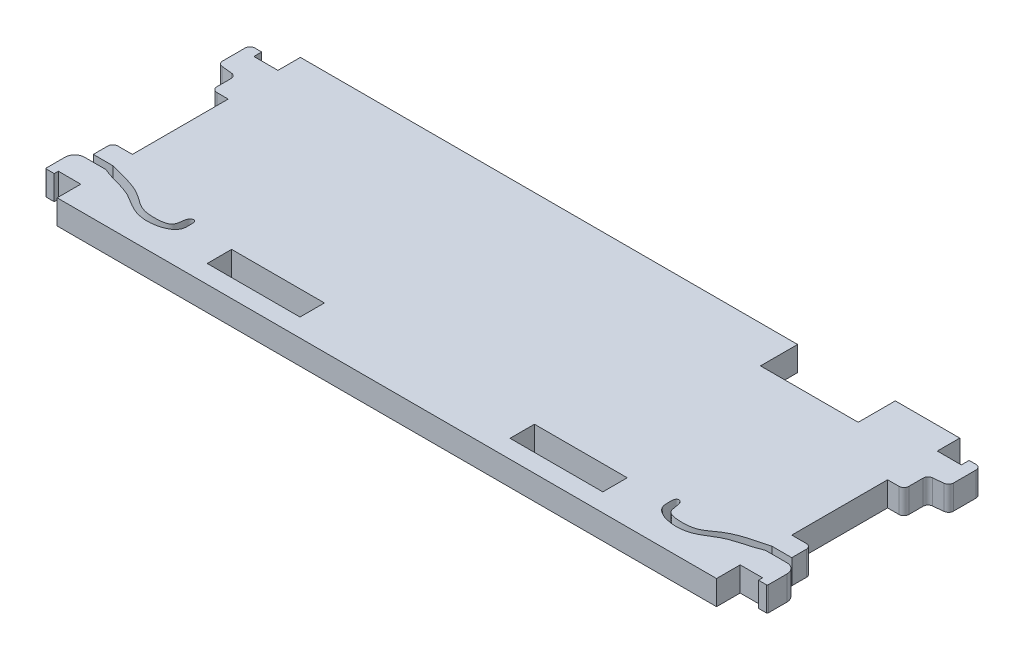
SolidWorks part; units mm, degrees
material "Custom Plastic"
ref_plane "Front Plane" through (0, 0, 0) normal (0, 0, 1) x (1, 0, 0)
ref_plane "Top Plane" through (0, 0, 0) normal (0, 1, 0) x (1, 0, 0)
ref_plane "Right Plane" through (0, 0, 0) normal (1, 0, 0) x (0, 0, -1)
sketch "Sketch1" plane through (0, 0, 0) normal (0, 1, 0) x (1, 0, 0)
  line L0 (34.4805, 15.8115) -> (34.4805, 10.9855)
  line L1 (-42.8625, -15.8115) -> (42.8625, -15.8115)
  line L2 (-42.8625, -15.8115) -> (-42.8625, -12.7381) construction
  line L3 (-42.8625, 15.8115) -> (21.7805, 15.8115)
  line L4 (42.8625, -15.8115) -> (42.8625, -12.7381)
  line L5 (-42.8625, -15.8115) -> (42.8625, 15.8115) construction
  line L6 (-42.8625, 15.8115) -> (42.8625, -15.8115) construction
  line L7 (34.4805, 10.9855) -> (21.7805, 10.9855)
  line L8 (21.7805, 10.9855) -> (21.7805, 15.8115)
  line L9 (34.4805, 15.8115) -> (42.8625, 15.8115)
  line L10 (13.6525, -10.2743) -> (13.6525, -13.4493)
  line L11 (13.6525, -13.4493) -> (25.7175, -13.4493)
  line L12 (25.7175, -13.4493) -> (25.7175, -10.2743)
  line L13 (25.7175, -10.2743) -> (13.6525, -10.2743)
  line L14 (0, 15.8115) -> (0, -15.8115) construction
  line L15 (-25.7175, -10.2743) -> (-13.6525, -10.2743)
  line L16 (-25.7175, -13.4493) -> (-25.7175, -10.2743)
  line L17 (-13.6525, -13.4493) -> (-25.7175, -13.4493)
  line L18 (-13.6525, -10.2743) -> (-13.6525, -13.4493)
  line L19 (42.8625, 12.8905) -> (45.9867, 12.8905)
  line L20 (45.9867, 12.8905) -> (45.9867, 13.9065)
  line L21 (45.9867, 13.9065) -> (46.8757, 13.9065)
  line L22 (47.5107, 13.2715) -> (47.5107, 10.3381)
  line L23 (46.9421, 9.7065) -> (45.5532, 9.5606)
  line L24 (44.9846, 8.929) -> (44.9846, 7.0624)
  line L25 (44.3496, 6.4274) -> (42.8625, 6.4274)
  line L26 (42.8625, 12.8905) -> (42.8625, 15.8115)
  line L27 (-44.3496, 6.4274) -> (-42.8625, 6.4274)
  line L28 (-42.8625, 12.8905) -> (-45.9867, 12.8905)
  line L29 (-44.9846, 8.929) -> (-44.9846, 7.0624)
  line L30 (-46.9421, 9.7065) -> (-45.5532, 9.5606)
  line L31 (-47.5107, 13.2715) -> (-47.5107, 10.3381)
  line L32 (-45.9867, 13.9065) -> (-46.8757, 13.9065)
  line L33 (-45.9867, 12.8905) -> (-45.9867, 13.9065)
  line L34 (-42.8625, 12.8905) -> (-42.8625, 15.8115)
  line L35 (-42.8625, -15.8115) -> (-42.8625, -12.7381)
  line L36 (-42.8625, -6.0325) -> (-44.7675, -6.0325)
  line L37 (-45.4025, -6.6675) -> (-45.4025, -8.5725)
  line L38 (-45.4025, -8.5725) -> (-42.8625, -8.5725)
  line L39 (-42.8625, -9.4615) -> (-45.2983, -9.4615)
  line L40 (-45.2983, -9.4615) -> (-45.6565, -9.4615)
  line L41 (-46.9265, -10.7315) -> (-46.9265, -13.1445)
  line L42 (-46.7995, -13.2715) -> (-45.7835, -13.2715)
  line L43 (-45.7835, -13.2715) -> (-45.7835, -12.7381)
  line L44 (-45.7835, -12.7381) -> (-42.8625, -12.7381)
  line L45 (45.7835, -12.7381) -> (42.8625, -12.7381)
  line L46 (-42.8625, -6.0325) -> (-42.8625, 6.4274)
  line L47 (45.7835, -13.2715) -> (45.7835, -12.7381)
  line L48 (46.7995, -13.2715) -> (45.7835, -13.2715)
  line L49 (46.9265, -10.7315) -> (46.9265, -13.1445)
  line L50 (45.2983, -9.4615) -> (45.6565, -9.4615)
  line L51 (42.8625, -9.4615) -> (45.2983, -9.4615)
  line L52 (45.4025, -8.5725) -> (42.8625, -8.5725)
  line L53 (45.4025, -6.6675) -> (45.4025, -8.5725)
  line L54 (42.8625, -6.0325) -> (44.7675, -6.0325)
  line L55 (42.8625, -6.0325) -> (42.8625, 6.4274)
  arc A0 (44.9846, 7.0624) -> (44.3496, 6.4274) centre (44.3496, 7.0624) cw
  arc A1 (44.9846, 8.929) -> (45.5532, 9.5606) centre (45.6196, 8.929) cw
  arc A2 (46.8757, 13.9065) -> (47.5107, 13.2715) centre (46.8757, 13.2715) cw
  arc A3 (47.5107, 10.3381) -> (46.9421, 9.7065) centre (46.8757, 10.3381) cw
  arc A4 (-44.9846, 7.0624) -> (-44.3496, 6.4274) centre (-44.3496, 7.0624) ccw
  arc A5 (-47.5107, 10.3381) -> (-46.9421, 9.7065) centre (-46.8757, 10.3381) ccw
  arc A6 (-46.8757, 13.9065) -> (-47.5107, 13.2715) centre (-46.8757, 13.2715) ccw
  arc A7 (-44.9846, 8.929) -> (-45.5532, 9.5606) centre (-45.6196, 8.929) ccw
  arc A8 (-45.6565, -9.4615) -> (-46.9265, -10.7315) centre (-45.6565, -10.7315) ccw
  arc A9 (-46.7995, -13.2715) -> (-46.9265, -13.1445) centre (-46.7995, -13.1445) cw
  arc A10 (-44.7675, -6.0325) -> (-45.4025, -6.6675) centre (-44.7675, -6.6675) ccw
  arc A11 (44.7675, -6.0325) -> (45.4025, -6.6675) centre (44.7675, -6.6675) cw
  arc A12 (46.7995, -13.2715) -> (46.9265, -13.1445) centre (46.7995, -13.1445) ccw
  arc A13 (45.6565, -9.4615) -> (46.9265, -10.7315) centre (45.6565, -10.7315) cw
  spline S0 degree 3 poles (-42.8625, -8.5725) (-41.2355, -9.0369) (-38.7684, -9.431) (-36.2864, -11.6153) (-34.3115, -11.8209) (-32.1595, -11.5627) (-32.1519, -10.2271) (-31.9015, -9.421) (-31.2167, -9.3607) (-31.1538, -10.3391) (-31.1859, -11.9202) (-33.9969, -12.8428) (-36.5674, -12.3054) (-39.1554, -10.3342) (-41.5136, -10.0774) (-42.8625, -9.4615) knots 0 0 0 0 0.185039 0.260037 0.340769 0.40557 0.445762 0.473511 0.483382 0.508842 0.55284 0.658675 0.754663 0.839419 1 1 1 1
  spline S1 degree 3 poles (42.8625, -8.5725) (41.2355, -9.0369) (38.7684, -9.431) (36.2864, -11.6153) (34.3115, -11.8209) (32.1595, -11.5627) (32.1519, -10.2271) (31.9015, -9.421) (31.2167, -9.3607) (31.1538, -10.3391) (31.1859, -11.9202) (33.9969, -12.8428) (36.5674, -12.3054) (39.1554, -10.3342) (41.5136, -10.0774) (42.8625, -9.4615) knots 0 0 0 0 0.185039 0.260037 0.340769 0.40557 0.445762 0.473511 0.483382 0.508842 0.55284 0.658675 0.754663 0.839419 1 1 1 1
  point P0 (0, 0)
  point P30 (44.9846, 6.4274)
  point P33 (44.9846, 9.5008)
  point P36 (47.5107, 13.9065)
  point P39 (47.5107, 9.7663)
  point P56 (-47.5107, 9.7663)
  point P57 (-47.5107, 13.9065)
  point P58 (-44.9846, 9.5008)
  point P59 (-44.9846, 6.4274)
  dimension "D18" = 0.635
  dimension "D19" = 0.635
  dimension "D20" = 0.635
  dimension "D21" = 0.635
  dimension "D25" = 1.27
  dimension "D26" = 0.127
  dimension "D27" = 0.635
  dimension "D1" = 85.725
  dimension "D2" = 31.623
  dimension "D3" = 8.382
  dimension "D4" = 12.7
  dimension "D5" = 4.826
  dimension "D6" = 17.145
  dimension "D7" = 3.175
  dimension "D8" = 12.065
  dimension "D9" = 2.3622
  dimension "D10" = 2.921
  dimension "D11" = 1.016
  dimension "D12" = 1.524
  dimension "D13" = 4.1402
  dimension "D14" = 2.54
  dimension "D15" = 3.0734
  dimension "D16" = 3.1242
  dimension "D17" = 96
  dimension "D22" = 4.064
  dimension "D23" = 0.5334
  dimension "D24" = 0.889
  dimension "D28" = 1.016
  dimension "D29" = 2.413
  dimension "D30" = 3.81
  dimension "D31" = 1.905
  dimension "D32" = 3.0734
  dimension "D33" = 0.3582
  dimension "D34" = 2.54
extrude "Boss-Extrude1" add sketch "Sketch1" along normal blind 3.175
